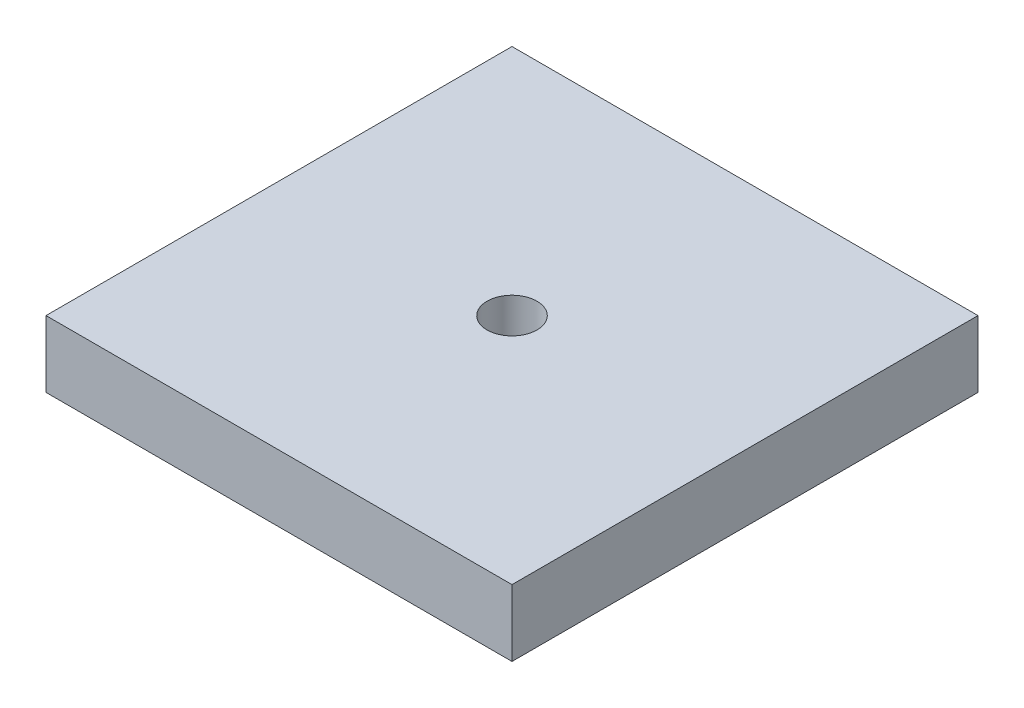
SolidWorks part; units mm, degrees
ref_plane "Front Plane" through (0, 0, 0) normal (0, 0, 1) x (1, 0, 0)
ref_plane "Top Plane" through (0, 0, 0) normal (0, 1, 0) x (1, 0, 0)
ref_plane "Right Plane" through (0, 0, 0) normal (1, 0, 0) x (0, 0, -1)
sketch "Sketch1" plane through (0, 0, 0) normal (0, 1, 0) x (1, 0, 0)
  line L1 (0, 0) -> (11.2, 0)
  line L2 (0, 0) -> (0, 11.2)
  line L3 (0, 11.2) -> (11.2, 11.2)
  line L4 (11.2, 0) -> (11.2, 11.2)
  dimension "D1" = 11.2
  dimension "D2" = 11.2
extrude "Boss-Extrude1" add sketch "Sketch1" along normal blind 1.6 contours L2 L1 L4 L3
sketch "Sketch2" plane through (0, 1.6, 0) normal (0, 1, 0) x (1, 0, 0)
  line L0 (0, 5.6) -> (11.2, 5.6) construction
  line L1 (0, 0) -> (0, 11.2) construction
  line L2 (11.2, 0) -> (11.2, 11.2) construction
  line L3 (5.6, 5.6) -> (5.6, 11.2) construction
  line L4 (0, 11.2) -> (11.2, 11.2) construction
  circle A0 centre (5.6, 5.6) radius 0.6
  dimension "D1" = 1.2
extrude "Cut-Extrude1" cut sketch "Sketch2" against normal blind 5
